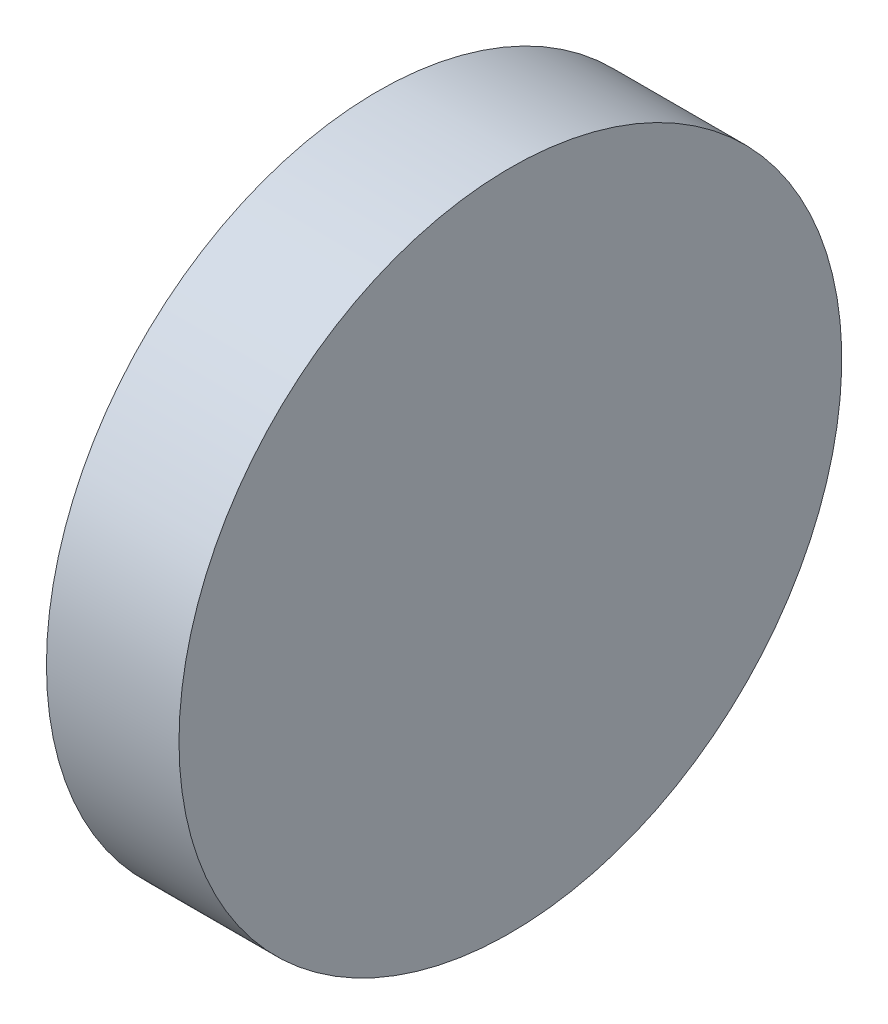
SolidWorks part; units mm, degrees
ref_plane "前视基准面" through (0, 0, 0) normal (0, 0, 1) x (1, 0, 0)
ref_plane "上视基准面" through (0, 0, 0) normal (0, 1, 0) x (1, 0, 0)
ref_plane "右视基准面" through (0, 0, 0) normal (1, 0, 0) x (0, 0, -1)
sketch "草图1" plane through (0, 0, 0) normal (0, 0, 1) x (1, 0, 0)
  line L0 (251.3749, 77.3114) -> (267.4051, 77.3114) construction
  line L1 (256.8849, 77.3114) -> (256.8849, 92.3114)
  line L2 (256.8849, 92.3114) -> (262.8849, 92.3114)
  line L3 (262.8849, 92.3114) -> (262.8849, 77.3114)
  line L4 (262.8849, 77.3114) -> (256.8849, 77.3114)
  dimension "D1" = 6
revolve "旋转1" add sketch "草图1" angle 360 about L0
